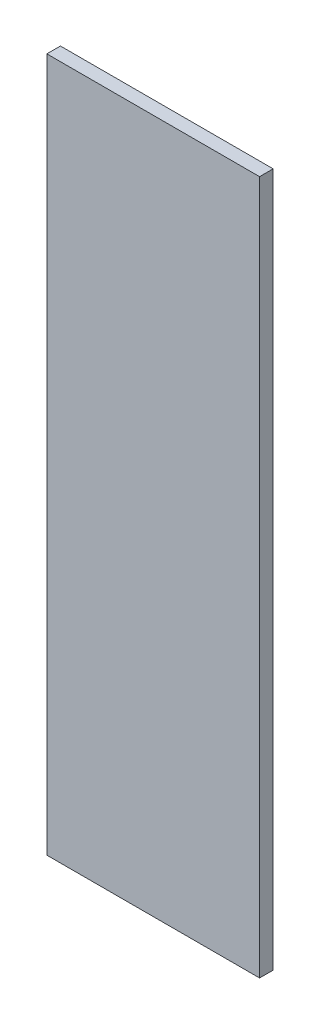
SolidWorks part; units mm, degrees
ref_plane "Спереди" through (0, 0, 0) normal (0, 0, 1) x (1, 0, 0)
ref_plane "Сверху" through (0, 0, 0) normal (0, 1, 0) x (1, 0, 0)
ref_plane "Справа" through (0, 0, 0) normal (1, 0, 0) x (0, 0, -1)
sketch "Эскиз1" plane through (0, 0, 0) normal (0, 0, 1) x (1, 0, 0)
  line L1 (141, -460) -> (-141, -460)
  line L2 (141, -460) -> (141, 460)
  line L3 (141, 460) -> (-141, 460)
  line L4 (-141, -460) -> (-141, 460)
  line L5 (141, -460) -> (-141, 460) construction
  line L6 (141, 460) -> (-141, -460) construction
  point P0 (0, 0)
  dimension "D1" = 920
  dimension "D2" = 282
extrude "Бобышка-Вытянуть1" add sketch "Эскиз1" along normal blind 18
